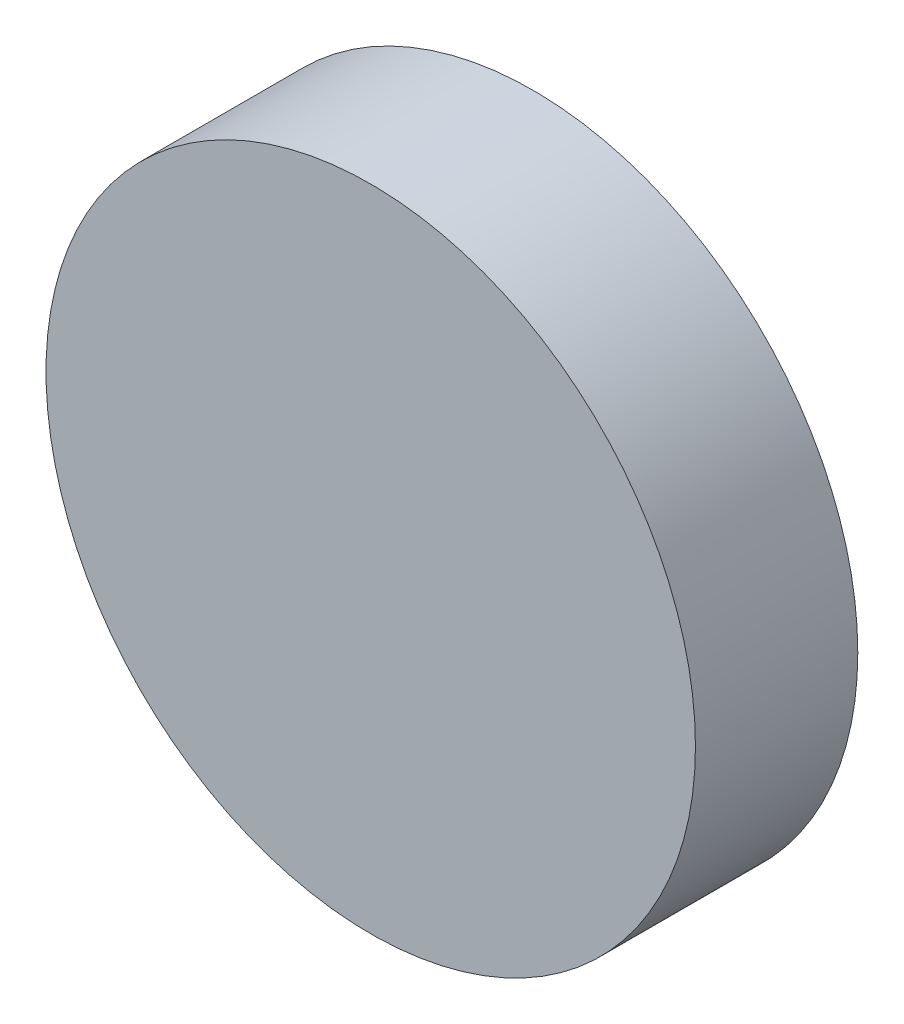
SolidWorks part; units mm, degrees
ref_plane "Front Plane" through (0, 0, 0) normal (0, 0, 1) x (1, 0, 0)
ref_plane "Top Plane" through (0, 0, 0) normal (0, 1, 0) x (1, 0, 0)
ref_plane "Right Plane" through (0, 0, 0) normal (1, 0, 0) x (0, 0, -1)
sketch "Sketch1" plane through (0, 0, 0) normal (0, 0, 1) x (1, 0, 0)
  circle A0 centre (0, 0) radius 12.7
  dimension "D1" = 25.4
extrude "Boss-Extrude1" add sketch "Sketch1" along normal blind 6.35
